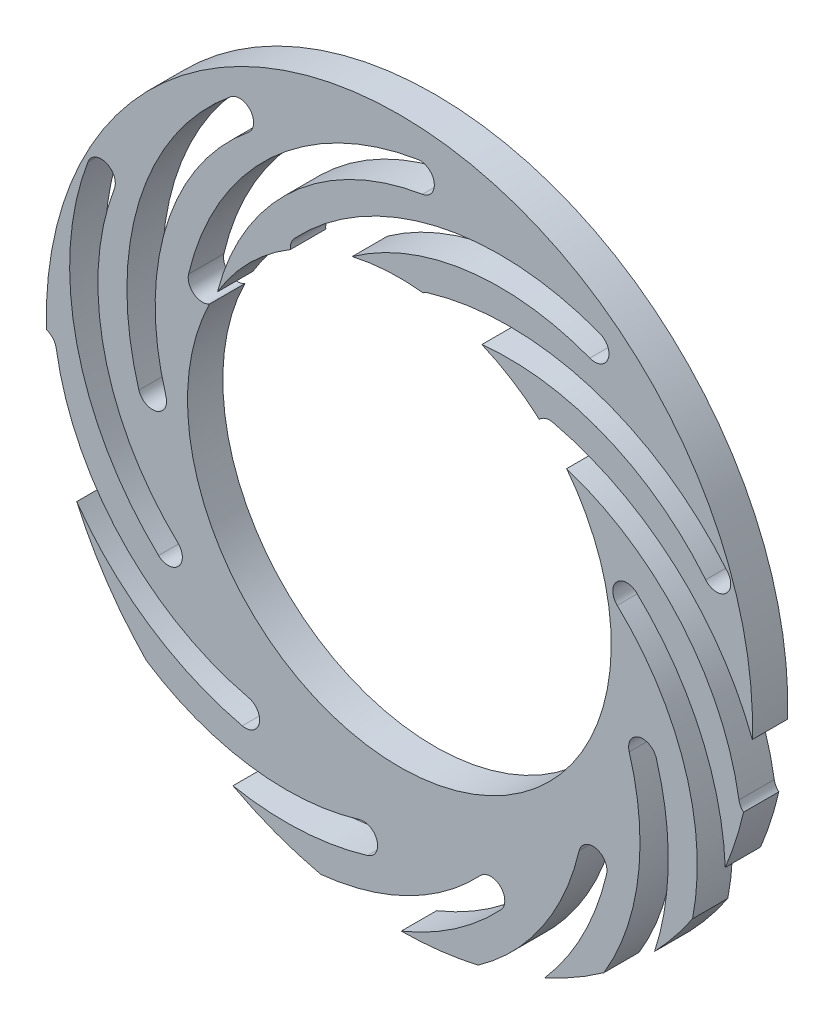
SolidWorks part; units mm, degrees
ref_plane "Front Plane" through (0, 0, 0) normal (0, 0, 1) x (1, 0, 0)
ref_plane "Top Plane" through (0, 0, 0) normal (0, 1, 0) x (1, 0, 0)
ref_plane "Right Plane" through (0, 0, 0) normal (1, 0, 0) x (0, 0, -1)
sketch "Sketch4" plane through (0, 0, 0) normal (0, 0, 1) x (1, 0, 0)
  line L0 (0, 0) -> (0.4032, 0) construction
  circle A0 centre (0, 0) radius 5
  circle A1 centre (0, 0) radius 3
  circle A2 centre (0, 0) radius 3.5 construction
  circle A3 centre (0, 0) radius 4.5 construction
  point P7 (0.9201, 0)
  point P8 (0.4032, 0)
  dimension "D1" = 10
  dimension "D2" = 6
  dimension "D3" = 0.5
  dimension "D4" = 0.5
sketch "Sketch5" plane through (0, 0, 0) normal (0, 0, 1) x (1, 0, 0)
  arc A0 (2.7675, 3.5484) -> (-1.343, 2.5986) centre (1.4224, 0) ccw construction
  circle A1 centre (0, 0) radius 4.5 construction
  arc A3 (2.8384, 3.7354) -> (-1.4888, 2.7356) centre (1.4224, 0) ccw
  arc A4 (2.6966, 3.3614) -> (-1.1973, 2.4617) centre (1.4224, 0) ccw
  arc A5 (2.6966, 3.3614) -> (2.8384, 3.7354) centre (2.7675, 3.5484) ccw
  arc A6 (-1.4888, 2.7356) -> (-1.1973, 2.4617) centre (-1.343, 2.5986) ccw
  arc A7 (4.3369, 1.4632) -> (0.5149, 2.6309) centre (1.5527, -0.8108) ccw
  arc A8 (4.3369, 1.4632) -> (4.6467, 1.7162) centre (4.4918, 1.5897) ccw
  arc A9 (0.3994, 3.0139) -> (0.5149, 2.6309) centre (0.4571, 2.8224) ccw
  arc A10 (4.6467, 1.7162) -> (0.3994, 3.0139) centre (1.5527, -0.8108) ccw
  arc A11 (4.4918, 1.5897) -> (0.4571, 2.8224) centre (1.5527, -0.8108) ccw construction
  arc A12 (4.8084, -1.0009) -> (2.0823, 1.9214) centre (1.2603, -1.5781) ccw
  arc A13 (4.8084, -1.0009) -> (5.2032, -0.9367) centre (5.0058, -0.9688) ccw
  arc A14 (2.1738, 2.3108) -> (2.0823, 1.9214) centre (2.128, 2.1161) ccw
  arc A15 (5.2032, -0.9367) -> (2.1738, 2.3108) centre (1.2603, -1.5781) ccw
  arc A16 (5.0058, -0.9688) -> (2.128, 2.1161) centre (1.2603, -1.5781) ccw construction
  arc A17 (3.9847, -3.3706) -> (3.085, 0.5233) centre (0.6233, -2.0964) ccw
  arc A18 (3.9847, -3.3706) -> (4.3587, -3.5124) centre (4.1717, -3.4415) ccw
  arc A19 (3.3589, 0.8148) -> (3.085, 0.5233) centre (3.222, 0.669) ccw
  arc A20 (4.3587, -3.5124) -> (3.3589, 0.8148) centre (0.6233, -2.0964) ccw
  arc A21 (4.1717, -3.4415) -> (3.222, 0.669) centre (0.6233, -2.0964) ccw construction
  arc A22 (2.0865, -5.0109) -> (3.2543, -1.1889) centre (-0.1874, -2.2267) ccw
  arc A23 (2.0865, -5.0109) -> (2.3395, -5.3207) centre (2.213, -5.1658) ccw
  arc A24 (3.6372, -1.0734) -> (3.2543, -1.1889) centre (3.4457, -1.1311) ccw
  arc A25 (2.3395, -5.3207) -> (3.6372, -1.0734) centre (-0.1874, -2.2267) ccw
  arc A26 (2.213, -5.1658) -> (3.4457, -1.1311) centre (-0.1874, -2.2267) ccw construction
  arc A27 (-0.3776, -5.4824) -> (2.5448, -2.7563) centre (-0.9548, -1.9343) ccw
  arc A28 (-0.3776, -5.4824) -> (-0.3134, -5.8772) centre (-0.3455, -5.6798) ccw
  arc A29 (2.9342, -2.8478) -> (2.5448, -2.7563) centre (2.7395, -2.802) ccw
  arc A30 (-0.3134, -5.8772) -> (2.9342, -2.8478) centre (-0.9548, -1.9343) ccw
  arc A31 (-0.3455, -5.6798) -> (2.7395, -2.802) centre (-0.9548, -1.9343) ccw construction
  arc A32 (-2.7473, -4.6587) -> (1.1466, -3.759) centre (-1.473, -1.2973) ccw
  arc A33 (-2.7473, -4.6587) -> (-2.8891, -5.0327) centre (-2.8182, -4.8457) ccw
  arc A34 (1.4381, -4.0329) -> (1.1466, -3.759) centre (1.2924, -3.896) ccw
  arc A35 (-2.8891, -5.0327) -> (1.4381, -4.0329) centre (-1.473, -1.2973) ccw
  arc A36 (-2.8182, -4.8457) -> (1.2924, -3.896) centre (-1.473, -1.2973) ccw construction
  arc A37 (-4.3876, -2.7605) -> (-0.5656, -3.9283) centre (-1.6034, -0.4866) ccw
  arc A38 (-4.3876, -2.7605) -> (-4.6974, -3.0135) centre (-4.5425, -2.887) ccw
  arc A39 (-0.4501, -4.3112) -> (-0.5656, -3.9283) centre (-0.5078, -4.1197) ccw
  arc A40 (-4.6974, -3.0135) -> (-0.4501, -4.3112) centre (-1.6034, -0.4866) ccw
  arc A41 (-4.5425, -2.887) -> (-0.5078, -4.1197) centre (-1.6034, -0.4866) ccw construction
  arc A42 (-4.8591, -0.2964) -> (-2.133, -3.2188) centre (-1.311, 0.2808) ccw
  arc A43 (-4.8591, -0.2964) -> (-5.2539, -0.3606) centre (-5.0565, -0.3285) ccw
  arc A44 (-2.2245, -3.6082) -> (-2.133, -3.2188) centre (-2.1787, -3.4135) ccw
  arc A45 (-5.2539, -0.3606) -> (-2.2245, -3.6082) centre (-1.311, 0.2808) ccw
  arc A46 (-5.0565, -0.3285) -> (-2.1787, -3.4135) centre (-1.311, 0.2808) ccw construction
  arc A47 (-4.0354, 2.0733) -> (-3.1357, -1.8206) centre (-0.674, 0.799) ccw
  arc A48 (-4.0354, 2.0733) -> (-4.4094, 2.2151) centre (-4.2224, 2.1442) ccw
  arc A49 (-3.4096, -2.1121) -> (-3.1357, -1.8206) centre (-3.2726, -1.9664) ccw
  arc A50 (-4.4094, 2.2151) -> (-3.4096, -2.1121) centre (-0.674, 0.799) ccw
  arc A51 (-4.2224, 2.1442) -> (-3.2726, -1.9664) centre (-0.674, 0.799) ccw construction
  arc A52 (-2.1372, 3.7136) -> (-3.3049, -0.1084) centre (0.1368, 0.9294) ccw
  arc A53 (-2.1372, 3.7136) -> (-2.3902, 4.0234) centre (-2.2637, 3.8685) ccw
  arc A54 (-3.6879, -0.2239) -> (-3.3049, -0.1084) centre (-3.4964, -0.1662) ccw
  arc A55 (-2.3902, 4.0234) -> (-3.6879, -0.2239) centre (0.1368, 0.9294) ccw
  arc A56 (-2.2637, 3.8685) -> (-3.4964, -0.1662) centre (0.1368, 0.9294) ccw construction
  arc A57 (0.3269, 4.1851) -> (-2.5954, 1.459) centre (0.9041, 0.6369) ccw
  arc A58 (0.3269, 4.1851) -> (0.2627, 4.5799) centre (0.2948, 4.3825) ccw
  arc A59 (-2.9848, 1.5505) -> (-2.5954, 1.459) centre (-2.7901, 1.5047) ccw
  arc A60 (0.2627, 4.5799) -> (-2.9848, 1.5505) centre (0.9041, 0.6369) ccw
  arc A61 (0.2948, 4.3825) -> (-2.7901, 1.5047) centre (0.9041, 0.6369) ccw construction
  point P8 (0.5681, 3.6974)
  point P13 (0, 0)
  point P19 (2.6616, 2.8184)
  point P27 (4.0351, 1.0104)
  point P35 (4.3207, -1.2421)
  point P43 (3.4417, -3.3356)
  point P51 (1.6338, -4.7091)
  point P59 (-0.6188, -4.9947)
  point P67 (-2.7123, -4.1157)
  point P75 (-4.0858, -2.3078)
  point P83 (-4.3714, -0.0552)
  point P91 (-3.4924, 2.0383)
  point P99 (-1.6844, 3.4118)
  point P104 (-0.0253, -0.6487)
  dimension "D3" = 12
extrude "Boss-Extrude2" add sketch "Sketch4" along normal blind 0.5
extrude "Cut-Extrude1" cut sketch "Sketch5" along normal blind 0.5
